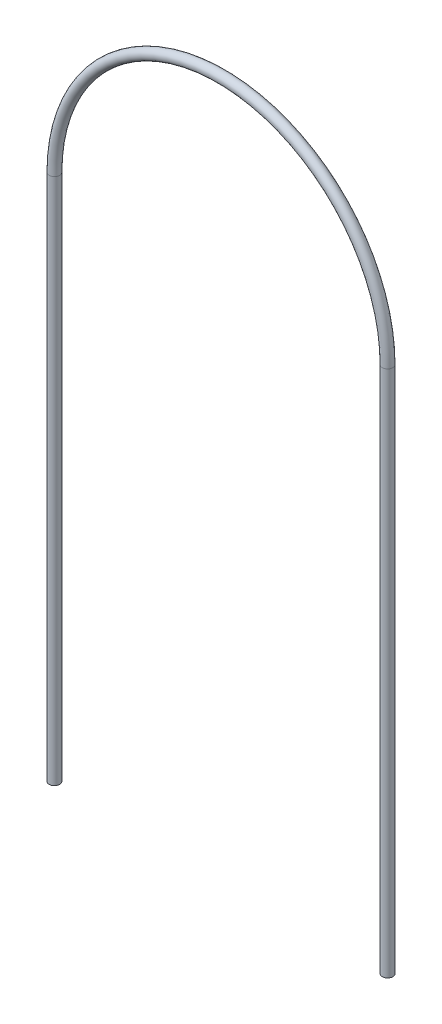
SolidWorks part; units mm, degrees
material "AISI 316 Stainless Steel Sheet (SS)"
ref_plane "Front Plane" through (0, 0, 0) normal (0, 0, 1) x (1, 0, 0)
ref_plane "Top Plane" through (0, 0, 0) normal (0, 1, 0) x (1, 0, 0)
ref_plane "Right Plane" through (0, 0, 0) normal (1, 0, 0) x (0, 0, -1)
ref_plane "Plane1" through (0, 215.9, 0) normal (0, -1, 0) x (1, 0, 0)
sketch "Sketch1" plane through (0, 215.9, 0) normal (0, -1, 0) x (1, 0, 0)
  line L0 (76.2, 2.413) -> (76.2, -2.413) construction
  circle A0 centre (152.4, 0) radius 2.413
revolve "Revolve1" add sketch "Sketch1" angle 180 about L0
sketch "Sketch2" plane through (0, 215.9, 0) normal (0, -1, 0) x (1, 0, 0)
  circle A0 centre (152.4, 0) radius 2.413
extrude "Boss-Extrude1" add sketch "Sketch2" along normal blind 241.3
sketch "Sketch3" plane through (0, 215.9, 0) normal (0, -1, 0) x (1, 0, 0)
  circle A0 centre (0, 0) radius 2.413
extrude "Boss-Extrude2" add sketch "Sketch3" along normal blind 241.3
